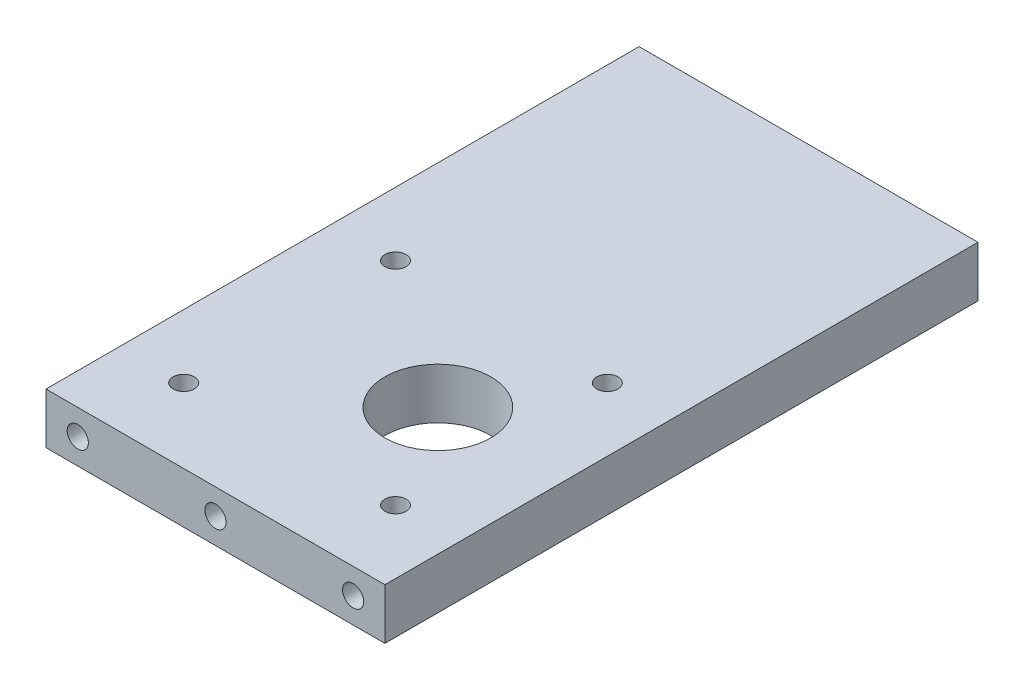
SolidWorks part; units mm, degrees
material "1.0545 (S355N)"
ref_plane "Front Plane" through (0, 0, 0) normal (0, 0, 1) x (1, 0, 0)
ref_plane "Top Plane" through (0, 0, 0) normal (0, 1, 0) x (1, 0, 0)
ref_plane "Right Plane" through (0, 0, 0) normal (1, 0, 0) x (0, 0, -1)
sketch "Sketch1" plane through (0, 0, 0) normal (0, 1, 0) x (1, 0, 0)
  line L0 (0, 0) -> (0, 140.817) construction
  line L1 (-40, 140) -> (40, 140)
  line L2 (-40, 140) -> (-40, 0)
  line L3 (-40, 0) -> (40, 0)
  line L4 (40, 140) -> (40, 0)
  circle A0 centre (10, 42.5) radius 12.5
  dimension "D4" = 25
  dimension "D1" = 80
  dimension "D2" = 140
  dimension "D3" = 97.5
  dimension "D5" = 30
extrude "Boss-Extrude1" add sketch "Sketch1" along normal mid plane 12
sketch "Sketch2" plane through (0, 6, 0) normal (0, 1, 0) x (1, 0, 0)
  line L0 (54.8315, 42.5) -> (-86.9211, 42.5) construction
  line L1 (0, 0) -> (0, 153.7848) construction
  line L2 (-40, 0) -> (40, 0) construction
  point P0 (25, 67.5)
  point P1 (-25, 67.5)
  point P2 (-25, 17.5)
  point P3 (25, 17.5)
  point P14 (10, 42.5)
  dimension "D1" = 50
  dimension "D3" = 50
hole_wizard "M6 Tapped Hole1" positions "Sketch3" profile "Sketch5" tap size "M6" standard "ISO" end condition through all
sketch "Sketch3" plane through (0, 6, 0) normal (0, 1, 0) x (1, 0, 0)
  point P0 (-25, 67.5)
  point P3 (25, 67.5)
  point P6 (25, 17.5)
  point P9 (-25, 17.5)
sketch "Sketch5" plane through (-25, 6, -67.5) normal (1, 0, 0) x (0, 0, 1)
  line L0 (0, 0) -> (0, 12)
  line L1 (0, 12) -> (2.5, 12)
  line L2 (2.5, 12) -> (2.5, 0)
  line L5 (2.5, 0) -> (0, 0)
  line L11 (0, -6.35) -> (0, 107.95) construction
  dimension "Thru Tap Drill Dia." = 5
  dimension "Thru Tap Drill Depth" = 12
cosmetic thread "Hole Thread1" parameters "D2"=6
cosmetic thread "Hole Thread2" parameters "D2"=6
cosmetic thread "Hole Thread3" parameters "D2"=6
cosmetic thread "Hole Thread4" parameters "D2"=6
sketch "Sketch7" plane through (0, 0, 0) normal (0, 0, 1) x (1, 0, 0)
  line L0 (34.4527, 0) -> (-37.6381, 0) construction
  line L3 (0, 12.2814) -> (0, -18.3619) construction
  point P3 (32.5, 0)
  point P4 (0, 0)
  point P6 (-32.5, 0)
  dimension "D1" = 65
hole_wizard "M6 Tapped Hole2" positions "Sketch8" profile "Sketch9" tap size "M6" standard "ISO"
sketch "Sketch8" plane through (0, 0, 0) normal (0, 0, 1) x (1, 0, 0)
  point P0 (32.5, 0)
  point P3 (0, 0)
  point P6 (-32.5, 0)
sketch "Sketch9" plane through (32.5, 0, 0) normal (1, 0, 0) x (0, -1, 0)
  line L0 (0, 0) -> (0, 14.5022)
  line L1 (0, 14.5022) -> (2.5, 13)
  line L2 (2.5, 13) -> (2.5, 0)
  line L5 (2.5, 0) -> (0, 0)
  line L10 (0, 14.5022) -> (-2.5, 13) construction
  line L11 (0, -6.35) -> (0, 107.95) construction
  dimension "Tap Drill Dia." = 5
  dimension "Tap Drill Depth" = 13
  dimension "Drill Angle" = 118
cosmetic thread "Hole Thread5" parameters "D1"=10, "D2"=6
cosmetic thread "Hole Thread6" parameters "D1"=10, "D2"=6
cosmetic thread "Hole Thread7" parameters "D1"=10, "D2"=6
ref_plane "Plane1" through (0, 0, -70) normal (0, 0, -1) x (-1, 0, 0)
mirror "Mirror1" about plane through (0, 0, -70) normal (0, 0, -1) of "M6 Tapped Hole2"
cosmetic thread "Hole Thread8" parameters "D1"=10, "D2"=6
cosmetic thread "Hole Thread9" parameters "D1"=10, "D2"=6
cosmetic thread "Hole Thread10" parameters "D1"=10, "D2"=6
sketch "Sketch10" plane through (-40, 0, 0) normal (-1, 0, 0) x (0, 0, 1)
  line L0 (0, 0) -> (-142.6132, 0) construction
  line L1 (-140, 6) -> (-140, -6) construction
  point P0 (-113, 0)
  point P1 (-86, 0)
  dimension "D2" = 27
  dimension "D4" = 27
hole_wizard "M8x1.0 Tapped Hole1" positions "Sketch11" profile "Sketch12" tap size "M8x1.0" standard "ISO"
sketch "Sketch11" plane through (-40, 0, 0) normal (-1, 0, 0) x (0, 0, 1)
  point P0 (-113, 0)
  point P3 (-86, 0)
sketch "Sketch12" plane through (-40, 0, -113) normal (0, 1, 0) x (0, 0, 1)
  line L0 (0, 0) -> (0, 21.103)
  line L1 (0, 21.103) -> (3.5, 19)
  line L2 (3.5, 19) -> (3.5, 0)
  line L5 (3.5, 0) -> (0, 0)
  line L10 (0, 21.103) -> (-3.5, 19) construction
  line L11 (0, -6.35) -> (0, 107.95) construction
  dimension "Tap Drill Dia." = 7
  dimension "Tap Drill Depth" = 19
  dimension "Drill Angle" = 118
cosmetic thread "Hole Thread13" parameters "D1"=16, "D2"=8
cosmetic thread "Hole Thread14" parameters "D1"=16, "D2"=8
